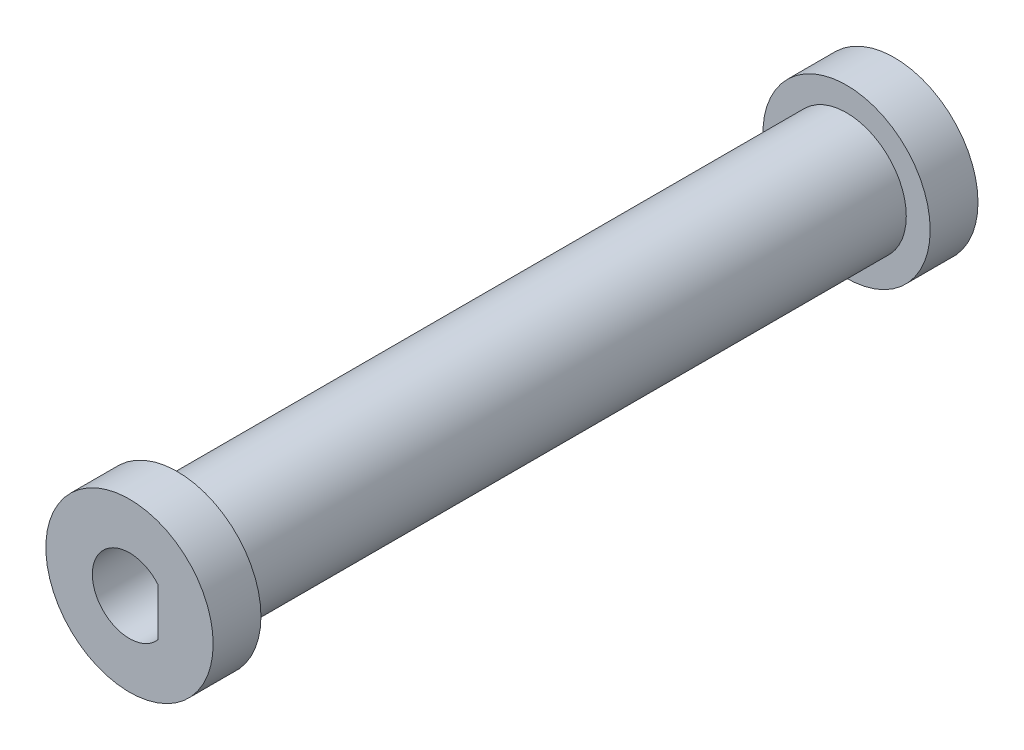
SolidWorks part; units mm, degrees
material "ABS"
ref_plane "Front Plane" through (0, 0, 0) normal (0, 0, 1) x (1, 0, 0)
ref_plane "Top Plane" through (0, 0, 0) normal (0, 1, 0) x (1, 0, 0)
ref_plane "Right Plane" through (0, 0, 0) normal (1, 0, 0) x (0, 0, -1)
sketch "Sketch1" plane through (0, 0, 0) normal (0, 0, 1) x (1, 0, 0)
  circle A0 centre (0, 0) radius 3.175
extrude "Boss-Extrude1" add sketch "Sketch1" along normal blind 35.56 contours A0
ref_plane "Plane1" through (0, 0, 17.78) normal (0, 0, 1) x (1, 0, 0)
sketch "Sketch3" plane through (0, 0, 35.56) normal (0, 0, 1) x (1, 0, 0)
  circle A0 centre (0, 0) radius 4.445
  dimension "D1" = 8.89
extrude "Boss-Extrude2" add sketch "Sketch3" along normal blind 2.54
mirror "Mirror1" about plane through (0, 0, 17.78) normal (0, 0, 1) of "Boss-Extrude2"
sketch "Sketch4" plane through (0, 0, 38.1) normal (0, 0, 1) x (1, 0, 0)
  line L0 (1.525, 0) -> (1.525, 1.255)
  line L1 (1.525, 0) -> (1.525, -1.255)
  arc A0 (1.525, 1.255) -> (1.525, -1.255) centre (0, 0) ccw
  dimension "D1" = 1.255
  dimension "D2" = 1.255
extrude "Cut-Extrude1" cut sketch "Sketch4" against normal blind 10.16 contours A0 L1 L0
